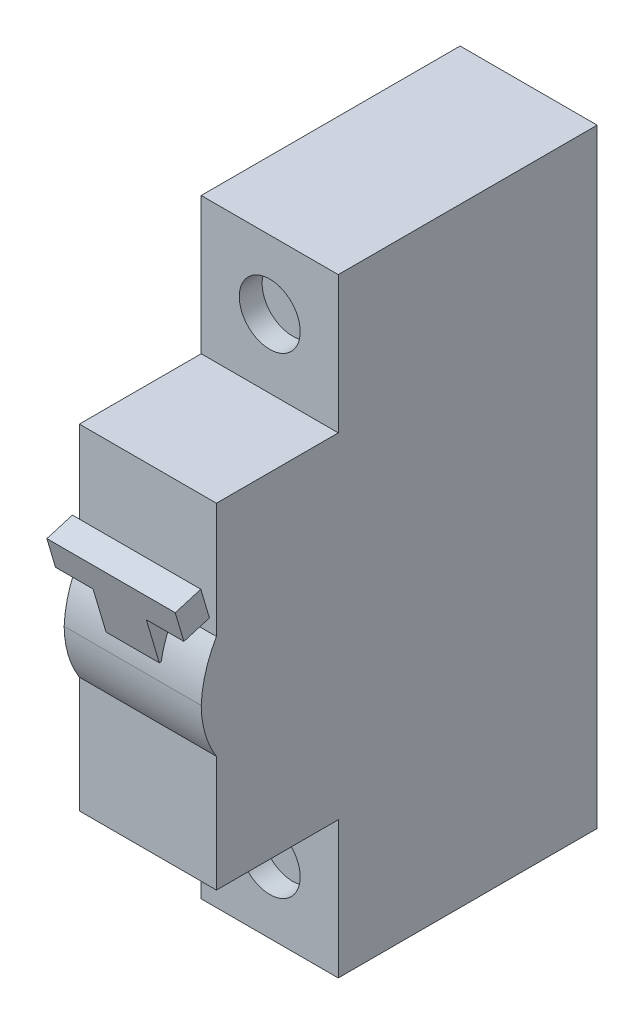
SolidWorks part; units mm, degrees
ref_plane "Alzado" through (0, 0, 0) normal (0, 0, 1) x (1, 0, 0)
ref_plane "Planta" through (0, 0, 0) normal (0, 1, 0) x (1, 0, 0)
ref_plane "Vista lateral" through (0, 0, 0) normal (1, 0, 0) x (0, 0, -1)
sketch "Croquis1" plane through (0, 0, 0) normal (0, 0, 1) x (1, 0, 0)
  line L1 (0, 0) -> (18, 0)
  line L2 (0, 0) -> (0, -80)
  line L3 (0, -80) -> (18, -80)
  line L4 (18, 0) -> (18, -80)
  dimension "D1" = 18
  dimension "D2" = 80
extrude "Saliente-Extruir1" add sketch "Croquis1" against normal blind 50
sketch "Croquis2" plane through (0, 0, 0) normal (-1, 0, 0) x (0, 0, 1)
  line L0 (-16, -18) -> (-16, -62) construction
  line L1 (0, 0) -> (-16, 0)
  line L2 (0, 0) -> (0, -18)
  line L3 (0, -18) -> (-16, -18)
  line L4 (-16, 0) -> (-16, -18)
  line L5 (0, -80) -> (-16, -80)
  line L6 (0, -80) -> (0, -62)
  line L7 (0, -62) -> (-16, -62)
  line L8 (-16, -80) -> (-16, -62)
  dimension "D1" = 18
  dimension "D2" = 18
  dimension "D3" = 16
extrude "Cortar-Extruir1" cut sketch "Croquis2" against normal blind 25
sketch "Croquis3" plane through (0, 0, 0) normal (-1, 0, 0) x (0, 0, 1)
  line L0 (0, -40) -> (2, -40) construction
  line L1 (0, -18) -> (0, -62) construction
  line L2 (0, -33.1583) -> (0, -46.7861)
  arc A0 (2, -40) -> (0, -33.1583) centre (-12.8034, -40.6143) ccw
  arc A1 (2, -40) -> (0, -46.7861) centre (-10.9699, -39.8652) cw
  dimension "D1" = 2
extrude "Saliente-Extruir2" add sketch "Croquis3" against normal up to surface (18 mm away) up to face at (18, -40, -20.5)
sketch "Croquis4" plane through (0, 0, 0) normal (0, 0, 1) x (1, 0, 0)
  line L0 (9, -33.1583) -> (9, -40) construction
  line L1 (18, -33.1583) -> (0, -33.1583) construction
  line L2 (18, -40) -> (0, -40) construction
  line L4 (5.5017, -37.906) -> (12.4983, -37.906)
  line L5 (5.5017, -37.906) -> (5.5017, -35.2523)
  line L6 (5.5017, -35.2523) -> (12.4983, -35.2523)
  line L7 (12.4983, -37.906) -> (12.4983, -35.2523)
  line L8 (5.5017, -37.906) -> (12.4983, -35.2523) construction
  line L9 (5.5017, -35.2523) -> (12.4983, -37.906) construction
  point P6 (9, -36.5792)
extrude "Saliente-Extruir3" add sketch "Croquis4" along normal blind 2
sketch "Croquis5" plane through (5.5017, 0, 0) normal (-1, 0, 0) x (0, 0, 1)
  line L0 (2, -37.906) -> (-1.3559, -36.912)
  line L1 (2, -37.906) -> (-1.1664, -37.906) construction
  line L2 (-1.3559, -36.912) -> (-0.4219, -33.759)
  line L3 (-0.4219, -33.759) -> (2.9339, -34.7531)
  line L4 (2.9339, -34.7531) -> (2, -37.906)
  dimension "D1" = 16.5
  dimension "D2" = 3.5
extrude "Cortar-Extruir2" cut sketch "Croquis5" against normal up to surface (6.9966 mm away) up to face at (12.4983, -36.5748, 1.7084)
sketch "Croquis6" plane through (0, -34.3037, -10.1612) normal (0, 0.9588, 0.284) x (1, 0, 0)
  line L1 (5.5017, -12.6835) -> (12.4983, -12.6835)
  line L2 (5.5017, -12.6835) -> (5.5017, -9.1835)
  line L3 (5.5017, -9.1835) -> (12.4983, -9.1835)
  line L4 (12.4983, -12.6835) -> (12.4983, -9.1835)
extrude "Saliente-Extruir4" add sketch "Croquis6" along normal blind 6
sketch "Croquis7" plane through (0, -28.5508, -8.4571) normal (0, 0.9588, 0.284) x (1, 0, 0)
  line L0 (9, -9.1835) -> (9, -12.6835) construction
  line L1 (12.4983, -9.1835) -> (5.5017, -9.1835) construction
  line L2 (5.5017, -12.6835) -> (12.4983, -12.6835) construction
  line L4 (0.5677, -9.1835) -> (17.4323, -9.1835)
  line L5 (0.5677, -9.1835) -> (0.5677, -12.6835)
  line L6 (0.5677, -12.6835) -> (17.4323, -12.6835)
  line L7 (17.4323, -9.1835) -> (17.4323, -12.6835)
  line L8 (0.5677, -9.1835) -> (17.4323, -12.6835) construction
  line L9 (0.5677, -12.6835) -> (17.4323, -9.1835) construction
  point P6 (9, -10.9335)
extrude "Saliente-Extruir5" add sketch "Croquis7" along normal blind 4
sketch "Croquis8" plane through (0, 0, -16) normal (0, 0, 1) x (1, 0, 0)
  line L0 (9, 0) -> (9, -18) construction
  line L1 (18, 0) -> (0, 0) construction
  line L2 (0, -18) -> (18, -18) construction
  line L3 (9, -80) -> (9, -62) construction
  line L4 (18, -80) -> (0, -80) construction
  line L5 (18, -62) -> (0, -62) construction
  circle A0 centre (9, -9) radius 4
  circle A1 centre (9, -71) radius 4
  dimension "D1" = 8
  dimension "D2" = 8
extrude "Cortar-Extruir3" cut sketch "Croquis8" against normal blind 3
